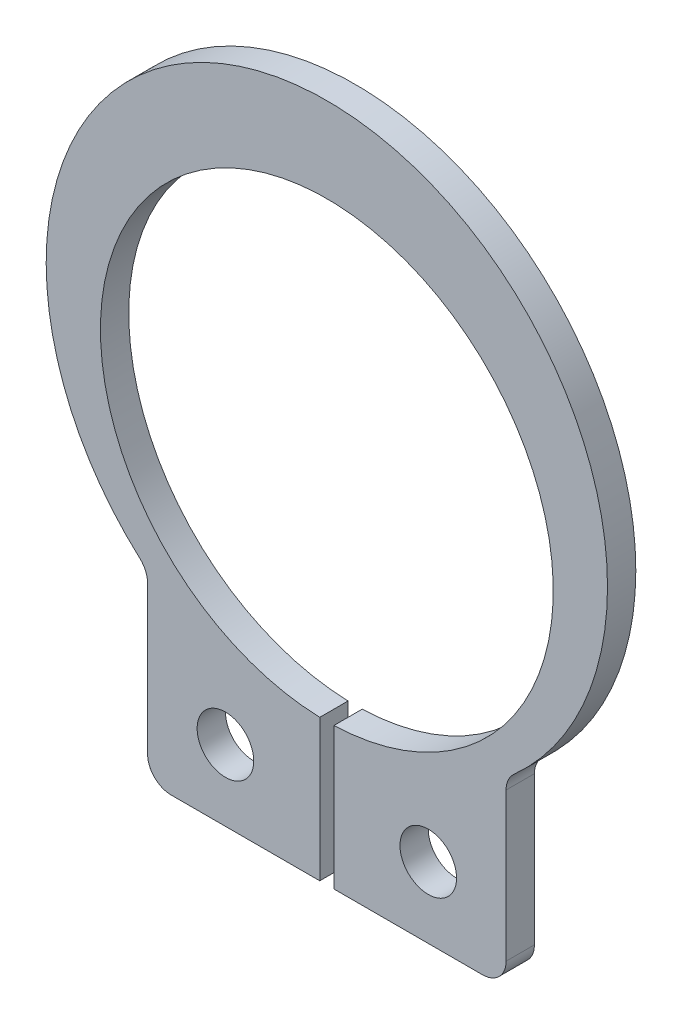
SolidWorks part; units mm, degrees
ref_plane "Front Plane" through (0, 0, 0) normal (0, 0, 1) x (1, 0, 0)
ref_plane "Top Plane" through (0, 0, 0) normal (0, 1, 0) x (1, 0, 0)
ref_plane "Right Plane" through (0, 0, 0) normal (1, 0, 0) x (0, 0, -1)
sketch "Sketch1" plane through (0, 0, 0) normal (0, 0, 1) x (1, 0, 0)
  line L0 (-3.8, -4.1575) -> (-3.8, -7.3)
  line L1 (-3.3, -7.8) -> (-0.15, -7.8)
  line L5 (-0.15, -7.8) -> (-0.15, -4.7977)
  line L6 (0.15, -4.7977) -> (0.15, -7.8)
  line L10 (0.15, -7.8) -> (3.3, -7.8)
  line L11 (3.8, -7.3) -> (3.8, -4.1575)
  line L12 (0, 0) -> (0, 6.6) construction
  arc A0 (3.9667, -3.7849) -> (-3.9667, -3.7849) centre (0, 0.65) ccw
  arc A1 (-3.9667, -3.7849) -> (-3.8, -4.1575) centre (-4.3, -4.1575) cw
  arc A2 (-3.8, -7.3) -> (-3.3, -7.8) centre (-3.3, -7.3) ccw
  arc A4 (-0.15, -4.7977) -> (0.15, -4.7977) centre (0, 0) cw
  arc A6 (3.3, -7.8) -> (3.8, -7.3) centre (3.3, -7.3) ccw
  arc A7 (3.8, -4.1575) -> (3.9667, -3.7849) centre (4.3, -4.1575) cw
  dimension "D1" = 0.3
  dimension "REC_D2_s" = 9.6
  dimension "D2" = 0.5
  dimension "D4" = 0.65
  dimension "REC_MSM_1" = 11.9
  dimension "D3" = 0.5
  dimension "REC_MSM_2" = 7.6
  dimension "REC_A_s" = 3
  dimension "REC_B_s" = 1.8
extrude "Boss-Extrude1" add sketch "Sketch1" against normal blind 0.6
sketch "Sketch2" plane through (0, 0, 0) normal (0, 0, 1) x (1, 0, 0)
  line L0 (-3.8, -6.3) -> (3.8, -6.3) construction
  line L1 (-3.8, -4.1575) -> (-3.8, -7.3) construction
  line L2 (3.8, -7.3) -> (3.8, -4.1575) construction
  line L3 (-3.3, -7.8) -> (-0.15, -7.8) construction
  line L4 (0, 0) -> (0, -7.8) construction
  circle A0 centre (-2.15, -6.3) radius 0.6
  circle A1 centre (2.15, -6.3) radius 0.6
  dimension "REC_D0_s" = 1.2
  dimension "REC_MSM_4" = 1.5
  dimension "REC_MSM_3" = 4.3
extrude "Cut-Extrude1" cut sketch "Sketch2" against normal through all
